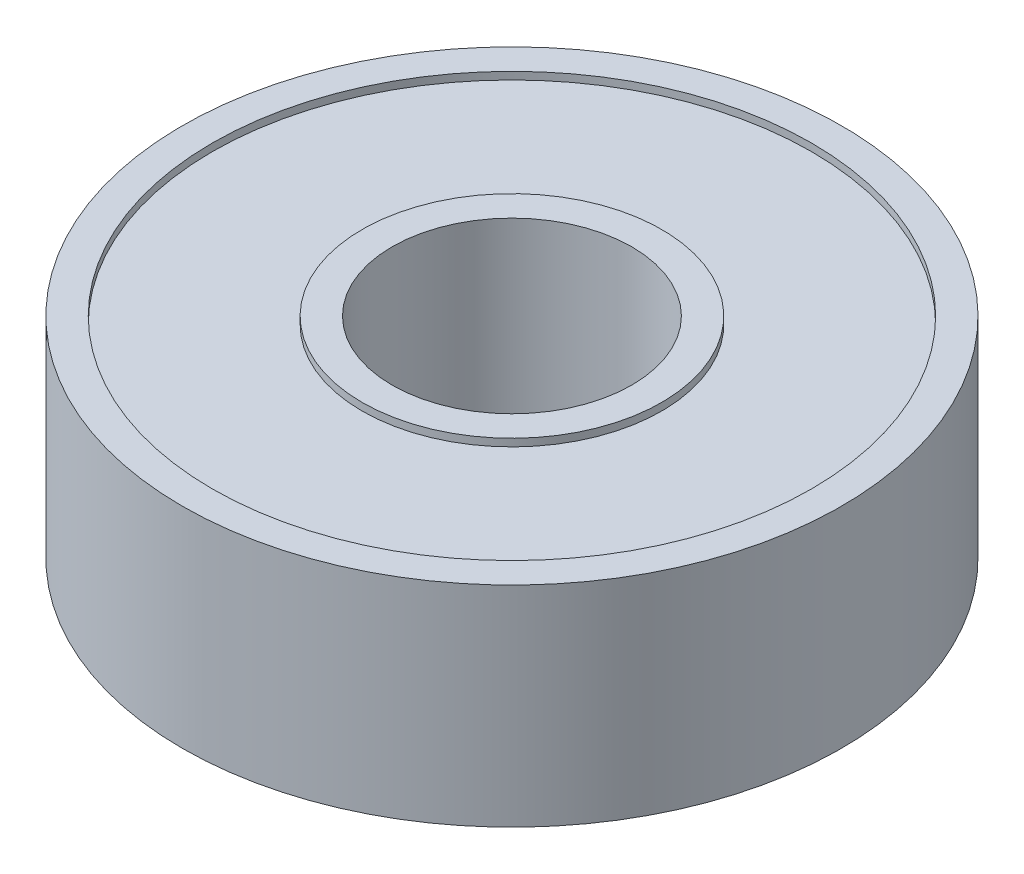
SolidWorks part; units mm, degrees
ref_plane "Front Plane" through (0, 0, 0) normal (0, 0, 1) x (1, 0, 0)
ref_plane "Top Plane" through (0, 0, 0) normal (0, 1, 0) x (1, 0, 0)
ref_plane "Right Plane" through (0, 0, 0) normal (1, 0, 0) x (0, 0, -1)
sketch "Sketch1" plane through (0, 0, 0) normal (0, 1, 0) x (1, 0, 0)
  circle A0 centre (0, 0) radius 11
  circle A1 centre (0, 0) radius 4
  dimension "D1" = 8
  dimension "D2" = 22
extrude "Boss-Extrude1" add sketch "Sketch1" along normal blind 7
sketch "Sketch2" plane through (0, 7, 0) normal (0, 1, 0) x (1, 0, 0)
  circle A0 centre (0, 0) radius 5
  circle A1 centre (0, 0) radius 10
  dimension "D1" = 20
  dimension "D2" = 10
extrude "Cut-Extrude1" cut sketch "Sketch2" against normal blind 0.25
ref_plane "Plane1" through (0, 3.5, 0) normal (0, 1, 0) x (1, 0, 0)
mirror "Mirror1" about plane through (0, 3.5, 0) normal (0, 1, 0) of "Cut-Extrude1"
